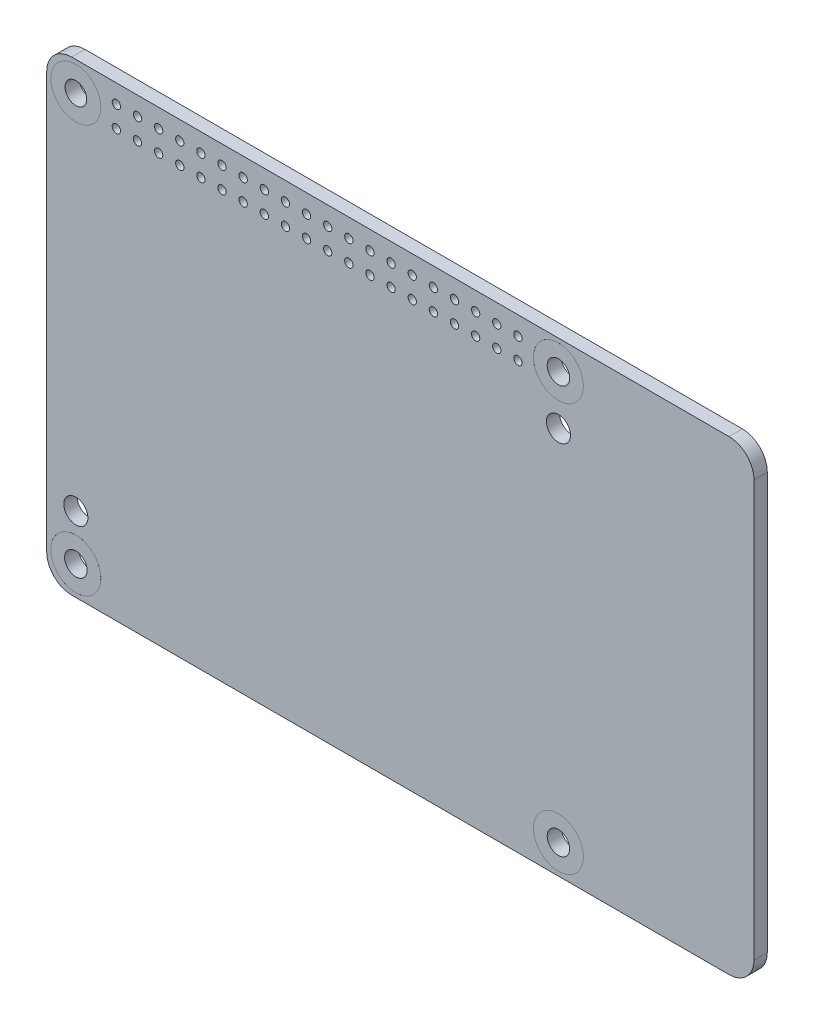
SolidWorks part; units mm, degrees
ref_plane "Płaszczyzna przednia" through (0, 0, 0) normal (0, 0, 1) x (1, 0, 0)
ref_plane "Płaszczyzna górna" through (0, 0, 0) normal (0, 1, 0) x (1, 0, 0)
ref_plane "Płaszczyzna prawa" through (0, 0, 0) normal (1, 0, 0) x (0, 0, -1)
sketch "Sketch1" plane through (0, 0, 0) normal (0, 0, 1) x (1, 0, 0)
  line L0 (-39.5, -28) -> (39.5, -28)
  line L1 (42.5, -25) -> (42.5, 25)
  line L2 (39.5, 28) -> (-39.5, 28)
  line L3 (-42.5, 25) -> (-42.5, -25)
  line L4 (0, -28) -> (0, 28) construction
  line L5 (153.0622, 295.5303) -> (1043.7288, 295.5303) construction
  arc A0 (39.5, -28) -> (42.5, -25) centre (39.5, -25) ccw
  arc A1 (42.5, 25) -> (39.5, 28) centre (39.5, 25) ccw
  arc A2 (-39.5, 28) -> (-42.5, 25) centre (-39.5, 25) ccw
  arc A3 (-42.5, -25) -> (-39.5, -28) centre (-39.5, -25) ccw
  dimension "D3" = 3
  dimension "D1" = 85
  dimension "D2" = 56
extrude "Boss-Extrude1" add sketch "Sketch1" along normal blind 1.6
sketch "Sketch3" plane through (0, 0, 1.6) normal (0, 0, 1) x (1, 0, 0)
  line L0 (-39, 28) -> (-39, 24.5) construction
  line L1 (39.5, 28) -> (-39.5, 28) construction
  line L2 (-39, 24.5) -> (-42.5, 24.5) construction
  line L4 (-42.5, 25) -> (-42.5, -25) construction
  line L5 (-42.5, 0) -> (-59.0247, 0) construction
  line L6 (-39, -24.5) -> (-42.5, -24.5) construction
  line L7 (-39, -28) -> (-39, -24.5) construction
  line L8 (-39, 24.5) -> (19, 24.5) construction
  line L9 (-10, 24.5) -> (-10, 38.9461) construction
  line L10 (19, -28) -> (19, -24.5) construction
  line L11 (19, -24.5) -> (22.5, -24.5) construction
  line L12 (22.5, 0) -> (39.0247, 0) construction
  line L13 (19, 24.5) -> (22.5, 24.5) construction
  line L14 (19, 28) -> (19, 24.5) construction
  circle A1 centre (-39, 24.5) radius 3
  circle A2 centre (-39, -24.5) radius 3
  circle A3 centre (19, -24.5) radius 3
  circle A4 centre (19, 24.5) radius 3
  dimension "D1" = 3.5
  dimension "D2" = 3.5
extrude "Cut-Extrude1" cut sketch "Sketch3" against normal through all
sketch "Sketch4" plane through (0, 0, 1.6) normal (0, 0, 1) x (1, 0, 0)
  circle A0 centre (-39, -24.5) radius 3 construction
  circle A1 centre (19, -24.5) radius 3 construction
  circle A2 centre (19, 24.5) radius 3 construction
  circle A3 centre (-39, 24.5) radius 3 construction
  circle A4 centre (-39, -24.5) radius 3
  circle A5 centre (19, -24.5) radius 3
  circle A6 centre (19, 24.5) radius 3
  circle A7 centre (-39, 24.5) radius 3
  circle A8 centre (-39, -24.5) radius 1.35
  circle A9 centre (19, -24.5) radius 1.35
  circle A10 centre (19, 24.5) radius 1.35
  circle A11 centre (-39, 24.5) radius 1.3
  dimension "D1" = 2.6
extrude "Boss-Extrude2" add sketch "Sketch4" against normal blind 1.7 separate body
sketch "Sketch5" plane through (0, 0, 1.6) normal (0, 0, 1) x (1, 0, 0)
  line L0 (-33, -28) -> (-33, -7.5) construction
  line L1 (-39.5, -28) -> (39.5, -28) construction
  line L2 (-42.5, -7.5) -> (-33, -7.5) construction
  line L3 (-42.5, 25) -> (-42.5, -25) construction
  line L4 (-33, -7.5) -> (-30.5, -7.5) construction
  line L5 (-30.5, -7.5) -> (-28, -7.5) construction
  circle A0 centre (-33, -7.5) radius 0.5
  circle A1 centre (-30.5, -7.5) radius 0.5
  circle A2 centre (-28, -7.5) radius 0.5
  dimension "D1" = 9.5
  dimension "D2" = 20.5
sketch "Sketch6" plane through (0, 0, 1.6) normal (0, 0, 1) x (1, 0, 0)
  line L0 (39.5, 28) -> (-39.5, 28) construction
  line L1 (-42.5, 25) -> (-42.5, -25) construction
  circle A0 centre (-34.13, 25.77) radius 0.5
  circle A1 centre (-34.13, 23.23) radius 0.5
  circle A2 centre (-31.59, 25.77) radius 0.5
  circle A3 centre (-31.59, 23.23) radius 0.5
  circle A4 centre (-29.05, 25.77) radius 0.5
  circle A5 centre (-29.05, 23.23) radius 0.5
  circle A6 centre (-26.51, 25.77) radius 0.5
  circle A7 centre (-26.51, 23.23) radius 0.5
  circle A8 centre (-23.97, 25.77) radius 0.5
  circle A9 centre (-23.97, 23.23) radius 0.5
  circle A10 centre (-21.43, 25.77) radius 0.5
  circle A11 centre (-21.43, 23.23) radius 0.5
  circle A12 centre (-18.89, 25.77) radius 0.5
  circle A13 centre (-18.89, 23.23) radius 0.5
  circle A14 centre (-16.35, 25.77) radius 0.5
  circle A15 centre (-16.35, 23.23) radius 0.5
  circle A16 centre (-13.81, 25.77) radius 0.5
  circle A17 centre (-13.81, 23.23) radius 0.5
  circle A18 centre (-11.27, 25.77) radius 0.5
  circle A19 centre (-11.27, 23.23) radius 0.5
  circle A20 centre (-8.73, 25.77) radius 0.5
  circle A21 centre (-8.73, 23.23) radius 0.5
  circle A22 centre (-6.19, 25.77) radius 0.5
  circle A23 centre (-6.19, 23.23) radius 0.5
  circle A24 centre (-3.65, 25.77) radius 0.5
  circle A25 centre (-3.65, 23.23) radius 0.5
  circle A26 centre (-1.11, 25.77) radius 0.5
  circle A27 centre (-1.11, 23.23) radius 0.5
  circle A28 centre (1.43, 25.77) radius 0.5
  circle A29 centre (1.43, 23.23) radius 0.5
  circle A30 centre (3.97, 25.77) radius 0.5
  circle A31 centre (3.97, 23.23) radius 0.5
  circle A32 centre (6.51, 25.77) radius 0.5
  circle A33 centre (6.51, 23.23) radius 0.5
  circle A34 centre (9.05, 25.77) radius 0.5
  circle A35 centre (9.05, 23.23) radius 0.5
  circle A36 centre (11.59, 25.77) radius 0.5
  circle A37 centre (11.59, 23.23) radius 0.5
  circle A38 centre (14.13, 25.77) radius 0.5
  circle A39 centre (14.13, 23.23) radius 0.5
  dimension "D1" = 2.54
  dimension "D2" = 1
  dimension "D3" = 2.23
  dimension "D4" = 8.37
  dimension "D5" = 20
extrude "Cut-Extrude3" cut sketch "Sketch6" against normal through all
sketch "Sketch7" plane through (0, 0, 1.6) normal (0, 0, 1) x (1, 0, 0)
  line L0 (42.5, -25) -> (42.5, 25) construction
  line L1 (39.5, 28) -> (-39.5, 28) construction
  circle A0 centre (20.27, 19.77) radius 0.5
  circle A1 centre (17.73, 19.77) radius 0.5
  circle A2 centre (17.73, 17.23) radius 0.5
  circle A3 centre (20.27, 17.23) radius 0.5
  dimension "D1" = 22.23
  dimension "D2" = 8.23
  dimension "D3" = 2.54
  dimension "D4" = 2.54
  dimension "D5" = 1
sketch "Szkic1" plane through (0, 0, 1.6) normal (0, 0, 1) x (1, 0, 0)
  line L0 (19, 24.5) -> (19, 18.6) construction
  line L1 (-39.5, -28) -> (39.5, -28) construction
  line L2 (-39, -24.5) -> (-39, -19) construction
  line L3 (-39, -24.5) -> (-39, 24.5) construction
  circle A0 centre (19, 18.6) radius 1.45
  circle A1 centre (-39, -19) radius 1.45
  dimension "D1" = 2.9
  dimension "D2" = 2.9
  dimension "D3" = 9
  dimension "D4" = 46.6
extrude "Wytnij-wyciągnięcie1" cut sketch "Szkic1" against normal through all
